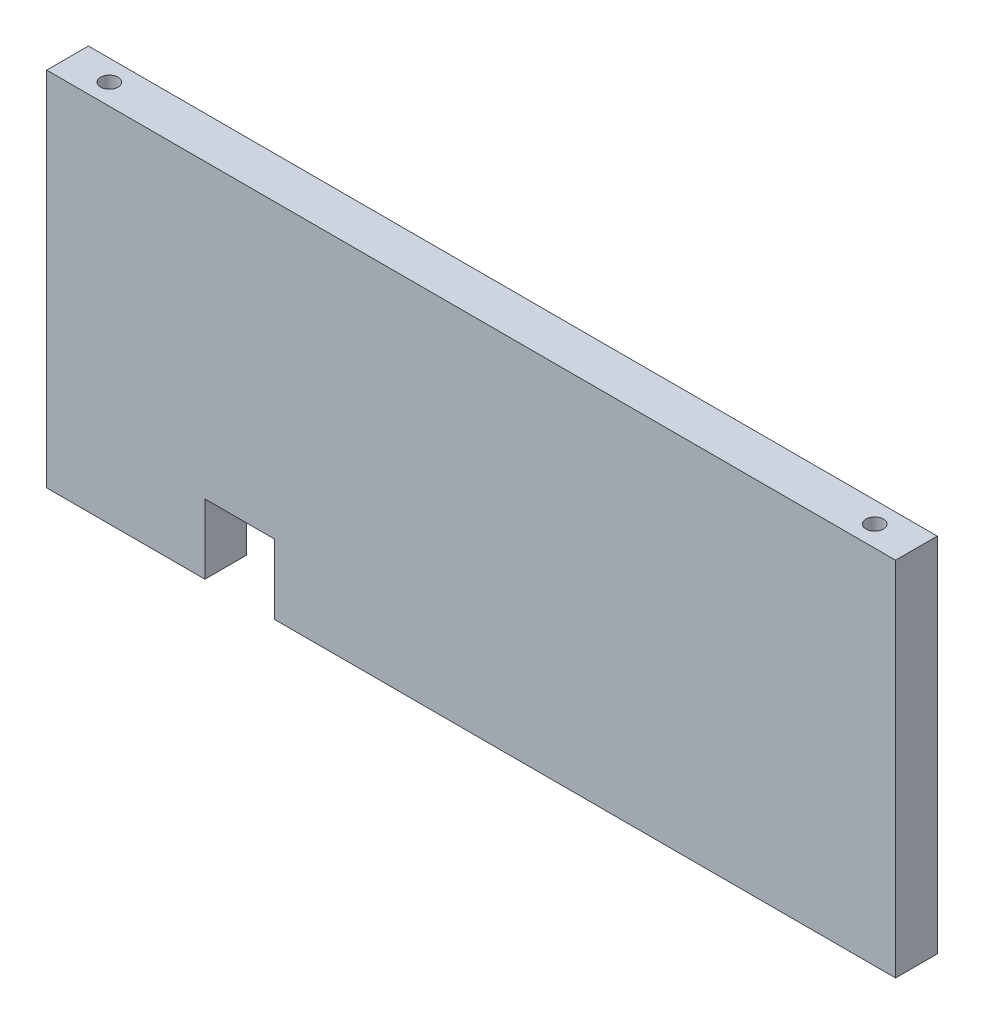
SolidWorks part; units mm, degrees
ref_plane "Front Plane" through (0, 0, 0) normal (0, 0, 1) x (1, 0, 0)
ref_plane "Top Plane" through (0, 0, 0) normal (0, 1, 0) x (1, 0, 0)
ref_plane "Right Plane" through (0, 0, 0) normal (1, 0, 0) x (0, 0, -1)
sketch "Sketch1" plane through (0, 0, 0) normal (0, 0, 1) x (1, 0, 0)
  line L0 (-55.7774, 27.8887) -> (66.2226, 27.8887)
  line L1 (66.2226, 27.8887) -> (66.2226, -24.1113)
  line L2 (66.2226, -24.1113) -> (-55.7774, -24.1113)
  line L3 (-55.7774, -24.1113) -> (-55.7774, 27.8887)
  dimension "D1" = 122
  dimension "D2" = 52
extrude "Boss-Extrude1" add sketch "Sketch1" against normal blind 6
sketch "Sketch2" plane through (0, 27.8887, 0) normal (0, 1, 0) x (1, 0, 0)
  line L0 (-55.7774, 6) -> (-55.7774, 0) construction
  line L1 (66.2226, 6) -> (-55.7774, 6) construction
  line L2 (66.2226, 6) -> (66.2226, 0) construction
  circle A0 centre (-49.7774, 3) radius 1.25
  circle A1 centre (60.2226, 3) radius 1.25
  dimension "D1" = 2.5
  dimension "D2" = 6
  dimension "D3" = 3
  dimension "D4" = 6
  dimension "D5" = 3
extrude "Cut-Extrude1" cut sketch "Sketch2" against normal through all
sketch "Sketch3" plane through (0, 0, -6) normal (0, 0, -1) x (-1, 0, 0)
  line L0 (23.0366, -24.1113) -> (23.0366, -14.1113)
  line L1 (55.7774, -24.1113) -> (-66.2226, -24.1113) construction
  line L2 (23.0366, -14.1113) -> (33.0366, -14.1113)
  line L3 (33.0366, -14.1113) -> (33.0366, -24.1113)
  line L4 (33.0366, -24.1113) -> (23.0366, -24.1113)
  dimension "D1" = 10
  dimension "D2" = 10
extrude "Cut-Extrude2" cut sketch "Sketch3" against normal blind 10
